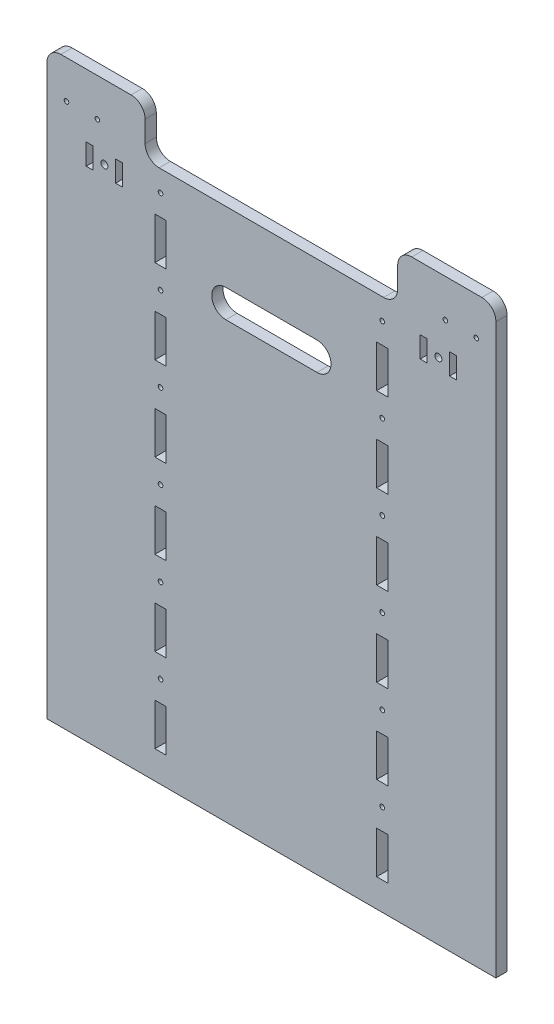
SolidWorks part; units mm, degrees
material "Acrylic (Medium-high impact)"
ref_plane "Front Plane" through (0, 0, 0) normal (0, 0, 1) x (1, 0, 0)
ref_plane "Top Plane" through (0, 0, 0) normal (0, 1, 0) x (1, 0, 0)
ref_plane "Right Plane" through (0, 0, 0) normal (1, 0, 0) x (0, 0, -1)
sketch "Sketch1" plane through (0, 0, 0) normal (0, 0, 1) x (1, 0, 0)
  line L0 (70, 380) -> (250, 380)
  line L1 (0, 0) -> (320, 0)
  line L2 (0, 0) -> (0, 415)
  line L3 (160, 380) -> (160, 0) construction
  line L4 (320, 0) -> (320, 415)
  line L6 (70, 415) -> (70, 380)
  line L7 (85, 50) -> (77, 50)
  line L8 (70, 415) -> (0, 415)
  line L9 (250, 415) -> (250, 380)
  line L10 (250, 415) -> (320, 415)
  line L12 (85, 50) -> (85, 20)
  line L13 (85, 20) -> (77, 20)
  line L14 (77, 50) -> (77, 20)
  line L18 (41, 362.5) -> (41, 356.3277) construction
  line L19 (28, 370) -> (33, 370)
  line L20 (28, 370) -> (28, 355)
  line L21 (28, 355) -> (33, 355)
  line L22 (33, 370) -> (33, 355)
  line L23 (49, 370) -> (49, 355)
  line L24 (54, 355) -> (49, 355)
  line L25 (54, 370) -> (54, 355)
  line L26 (54, 370) -> (49, 370)
  line L27 (279, 362.5) -> (279, 356.3277) construction
  line L28 (266, 370) -> (271, 370)
  line L29 (266, 370) -> (266, 355)
  line L30 (266, 355) -> (271, 355)
  line L31 (271, 370) -> (271, 355)
  line L32 (287, 370) -> (287, 355)
  line L33 (292, 355) -> (287, 355)
  line L34 (292, 370) -> (292, 355)
  line L35 (292, 370) -> (287, 370)
  line L67 (243, 50) -> (235, 50)
  line L68 (243, 50) -> (243, 20)
  line L69 (243, 20) -> (235, 20)
  line L70 (235, 50) -> (235, 20)
  line L71 (85, 110) -> (77, 110)
  line L72 (85, 110) -> (85, 80)
  line L73 (85, 80) -> (77, 80)
  line L74 (77, 110) -> (77, 80)
  line L75 (243, 110) -> (235, 110)
  line L76 (243, 110) -> (243, 80)
  line L77 (243, 80) -> (235, 80)
  line L78 (235, 110) -> (235, 80)
  line L79 (85, 170) -> (77, 170)
  line L80 (85, 170) -> (85, 140)
  line L81 (85, 140) -> (77, 140)
  line L82 (77, 170) -> (77, 140)
  line L83 (243, 170) -> (235, 170)
  line L84 (243, 170) -> (243, 140)
  line L85 (243, 140) -> (235, 140)
  line L86 (235, 170) -> (235, 140)
  line L87 (85, 230) -> (77, 230)
  line L88 (85, 230) -> (85, 200)
  line L89 (85, 200) -> (77, 200)
  line L90 (77, 230) -> (77, 200)
  line L91 (243, 230) -> (235, 230)
  line L92 (243, 230) -> (243, 200)
  line L93 (243, 200) -> (235, 200)
  line L94 (235, 230) -> (235, 200)
  line L95 (85, 290) -> (77, 290)
  line L96 (85, 290) -> (85, 260)
  line L97 (85, 260) -> (77, 260)
  line L98 (77, 290) -> (77, 260)
  line L99 (243, 290) -> (235, 290)
  line L100 (243, 290) -> (243, 260)
  line L101 (243, 260) -> (235, 260)
  line L102 (235, 290) -> (235, 260)
  line L111 (85, 387.5) -> (77, 387.5) [skipped]
  line L112 (85, 387.5) -> (85, 357.5) [skipped]
  line L113 (85, 357.5) -> (77, 357.5) [skipped]
  line L114 (77, 387.5) -> (77, 357.5) [skipped]
  line L115 (243, 387.5) -> (235, 387.5) [skipped]
  line L116 (243, 387.5) -> (243, 357.5) [skipped]
  line L117 (243, 357.5) -> (235, 357.5) [skipped]
  line L118 (235, 387.5) -> (235, 357.5) [skipped]
  line L119 (77, 320) -> (77, 290) [skipped]
  line L120 (235, 320) -> (235, 290) [skipped]
  line L121 (85, 290) -> (77, 290) [skipped]
  line L122 (243, 290) -> (235, 290) [skipped]
  line L123 (85, 320) -> (85, 290) [skipped]
  line L124 (243, 320) -> (243, 290) [skipped]
  line L125 (85, 320) -> (77, 320) [skipped]
  line L126 (243, 320) -> (235, 320) [skipped]
  line L127 (77, 252.5) -> (77, 222.5) [skipped]
  line L128 (235, 252.5) -> (235, 222.5) [skipped]
  line L129 (85, 222.5) -> (77, 222.5) [skipped]
  line L130 (243, 222.5) -> (235, 222.5) [skipped]
  line L131 (85, 252.5) -> (85, 222.5) [skipped]
  line L132 (243, 252.5) -> (243, 222.5) [skipped]
  line L133 (85, 252.5) -> (77, 252.5) [skipped]
  line L134 (243, 252.5) -> (235, 252.5) [skipped]
  line L135 (77, 185) -> (77, 155) [skipped]
  line L136 (235, 185) -> (235, 155) [skipped]
  line L137 (85, 155) -> (77, 155) [skipped]
  line L138 (243, 155) -> (235, 155) [skipped]
  line L139 (85, 185) -> (85, 155) [skipped]
  line L140 (243, 185) -> (243, 155) [skipped]
  line L141 (85, 185) -> (77, 185) [skipped]
  line L142 (243, 185) -> (235, 185) [skipped]
  line L143 (77, 117.5) -> (77, 87.5) [skipped]
  line L144 (235, 117.5) -> (235, 87.5) [skipped]
  line L145 (85, 87.5) -> (77, 87.5) [skipped]
  line L146 (243, 87.5) -> (235, 87.5) [skipped]
  line L147 (85, 117.5) -> (85, 87.5) [skipped]
  line L148 (243, 117.5) -> (243, 87.5) [skipped]
  line L149 (85, 117.5) -> (77, 117.5) [skipped]
  line L150 (243, 117.5) -> (235, 117.5) [skipped]
  line L151 (235, 50) -> (235, 20) [skipped]
  line L152 (243, 20) -> (235, 20) [skipped]
  line L153 (243, 50) -> (243, 20) [skipped]
  line L154 (243, 50) -> (235, 50) [skipped]
  line L155 (85, 350) -> (77, 350)
  line L156 (85, 350) -> (85, 320)
  line L157 (85, 320) -> (77, 320)
  line L158 (77, 350) -> (77, 320)
  line L159 (243, 350) -> (235, 350)
  line L160 (243, 350) -> (243, 320)
  line L161 (243, 320) -> (235, 320)
  line L162 (235, 350) -> (235, 320)
  circle A0 centre (14, 388) radius 1.625
  circle A1 centre (36, 388) radius 1.625
  circle A2 centre (41, 362.5) radius 2.5
  circle A3 centre (279, 362.5) radius 2.5
  circle A4 centre (284, 388) radius 1.625
  circle A5 centre (306, 388) radius 1.625
  circle A6 centre (239, 365) radius 1.65
  circle A7 centre (81, 365) radius 1.65
  circle A8 centre (239, 305) radius 1.65
  circle A9 centre (81, 305) radius 1.65
  circle A10 centre (239, 245) radius 1.65
  circle A11 centre (81, 245) radius 1.65
  circle A12 centre (239, 185) radius 1.65
  circle A13 centre (81, 185) radius 1.65
  circle A14 centre (239, 125) radius 1.65
  circle A15 centre (81, 125) radius 1.65
  circle A16 centre (239, 65) radius 1.65
  circle A17 centre (81, 65) radius 1.65
  point P31 (33, 362.5)
  point P37 (49, 362.5)
  point P51 (271, 362.5)
  point P52 (287, 362.5)
  dimension "D6" = 52.5
  dimension "D8" = 5
  dimension "D7" = 22
  dimension "D9" = 27
  dimension "D4" = 3.25
  dimension "D5" = 3.25
  dimension "D20" = 3.3
  dimension "D2" = 320
  dimension "D3" = 415
  dimension "D10" = 124
  dimension "D11" = 150
  dimension "D13" = 119
  dimension "D14" = 5
  dimension "D15" = 8
  dimension "D16" = 15
  dimension "D17" = 2
  dimension "D18" = 180
  dimension "D19" = 5
  dimension "D12" = 8
  dimension "D21" = 30
  dimension "D22" = 20
  dimension "D23" = 6
  dimension "D24" = 35
  dimension "D25" = 2
  dimension "D26" = 2
  dimension "D28" = 6
extrude "Boss-Extrude1" add sketch "Sketch1" along normal blind 8
fillet "Fillet1" radius 10 6 edges at (320, 415, 4) (250, 415, 4) (250, 380, 4) (70, 380, 4) (70, 415, 4) (0, 415, 4)
sketch "Sketch2" plane through (0, 0, 8) normal (0, 0, 1) x (1, 0, 0)
  line L0 (127.5, 320) -> (192.5, 320) construction
  line L1 (127.5, 330) -> (192.5, 330)
  line L2 (127.5, 310) -> (192.5, 310)
  line L3 (160, 380) -> (160, 0) construction
  line L4 (240, 380) -> (80, 380) construction
  line L5 (0, 0) -> (320, 0) construction
  arc A0 (127.5, 330) -> (127.5, 310) centre (127.5, 320) ccw
  arc A1 (192.5, 310) -> (192.5, 330) centre (192.5, 320) ccw
  point P2 (160, 320)
  dimension "D2" = 10
  dimension "D1" = 65
  dimension "D3" = 320
extrude "Cut-Extrude1" cut sketch "Sketch2" against normal through all
